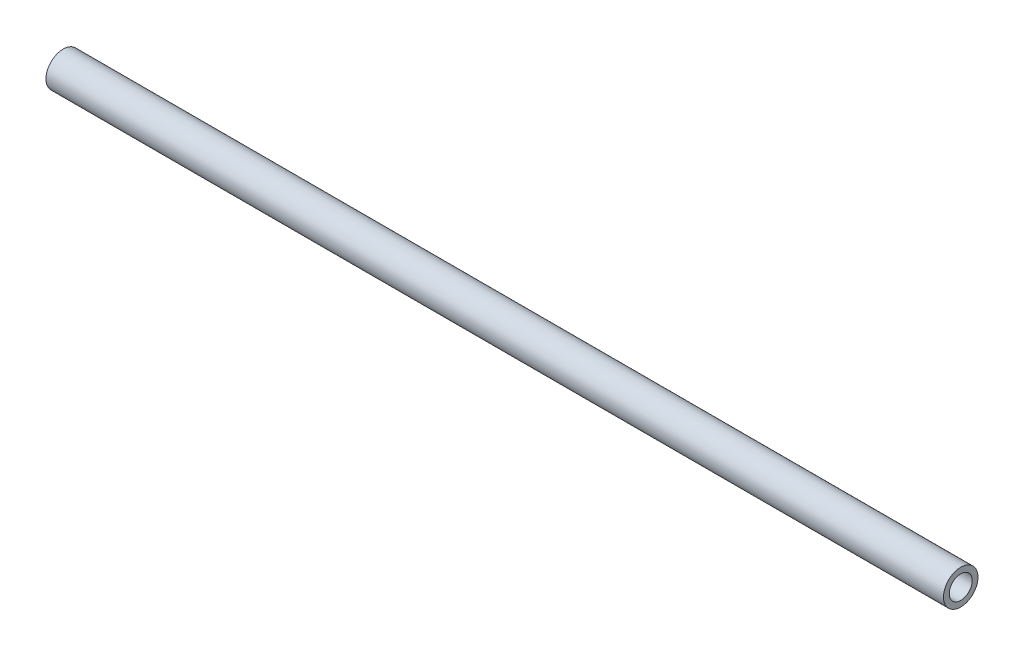
SolidWorks part; units mm, degrees
ref_plane "Front Plane" through (0, 0, 0) normal (0, 0, 1) x (1, 0, 0)
ref_plane "Top Plane" through (0, 0, 0) normal (0, 1, 0) x (1, 0, 0)
ref_plane "Right Plane" through (0, 0, 0) normal (1, 0, 0) x (0, 0, -1)
sketch "Sketch1" plane through (0, 0, 0) normal (1, 0, 0) x (0, 0, -1)
  circle A0 centre (0, 0) radius 9.525
  circle A1 centre (0, 0) radius 6.35
  dimension "D1" = 19.05
  dimension "D2" = 3.175
extrude "Boss-Extrude1" add sketch "Sketch1" against normal blind 495.3 contours A0 A1
move or copy body "Body-Move/Copy1" [suppressed] bodies to move or copy 101 parameters "D1"=0, "D2"=0, "D3"=0
move or copy body "Body-Move/Copy2" [suppressed] bodies to move or copy 102 parameters "D1"=0, "D2"=0, "D3"=0
